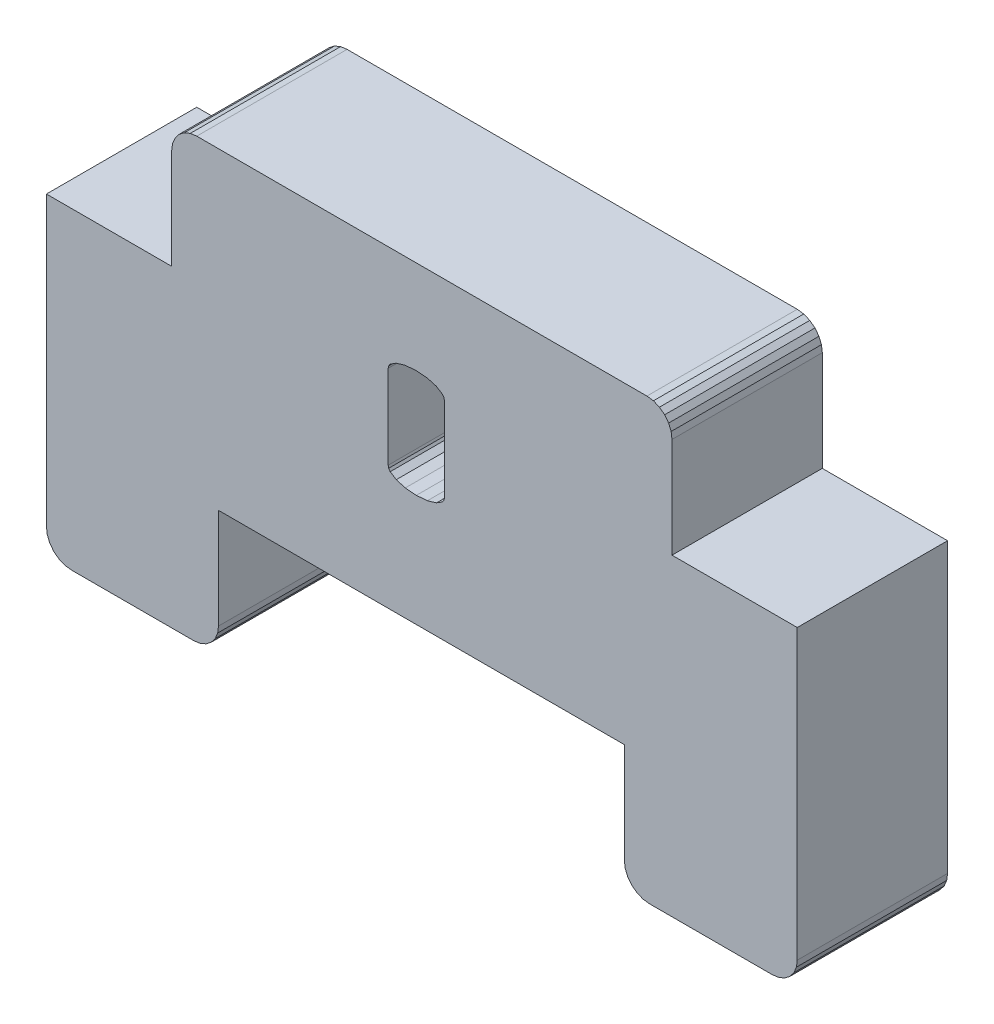
SolidWorks part; units mm, degrees
material "Maple"
ref_plane "Front Plane" through (0, 0, 0) normal (0, 0, 1) x (1, 0, 0)
ref_plane "Top Plane" through (0, 0, 0) normal (0, 1, 0) x (1, 0, 0)
ref_plane "Right Plane" through (0, 0, 0) normal (1, 0, 0) x (0, 0, -1)
sketch "Sketch1" plane through (0, 0, 0) normal (0, 0, 1) x (1, 0, 0)
  line L271 (-389.2048, -169.8544) -> (-389.1707, -169.5955)
  line L272 (-388.7048, -168.9883) -> (-388.4636, -168.8884)
  line L273 (-389.0708, -169.3544) -> (-388.9119, -169.1473)
  line L274 (-389.1707, -169.5955) -> (-389.0708, -169.3544)
  line L275 (-393.4636, -186.3203) -> (-393.7048, -186.2204)
  line L276 (-394.0708, -185.8544) -> (-394.1707, -185.6132)
  line L277 (-370.1363, -186.3544) -> (-370.3952, -186.3203)
  line L278 (-369.9775, -168.8884) -> (-370.2363, -168.8544)
  line L279 (-364.2363, -185.3544) -> (-364.2363, -173.8544)
  line L280 (-393.9119, -186.0615) -> (-394.0708, -185.8544)
  line L281 (-393.7048, -186.2204) -> (-393.9119, -186.0615)
  line L282 (-369.2363, -173.8544) -> (-364.2363, -173.8544)
  line L283 (-369.2363, -169.8544) -> (-369.2363, -173.8544)
  line L284 (-369.2363, -169.8544) -> (-369.2704, -169.5955)
  line L285 (-369.2704, -169.5955) -> (-369.3703, -169.3544)
  line L286 (-369.3703, -169.3544) -> (-369.5292, -169.1473)
  line L287 (-369.5292, -169.1473) -> (-369.7363, -168.9883)
  line L288 (-369.7363, -168.9883) -> (-369.9775, -168.8884)
  line L289 (-388.2048, -168.8544) -> (-370.2363, -168.8544)
  line L290 (-388.4636, -168.8884) -> (-388.2048, -168.8544)
  line L291 (-388.9119, -169.1473) -> (-388.7048, -168.9883)
  line L292 (-389.2048, -173.8544) -> (-389.2048, -169.8544)
  line L293 (-394.2048, -173.8544) -> (-389.2048, -173.8544)
  line L294 (-394.2048, -173.8544) -> (-394.2048, -185.3544)
  line L295 (-394.1707, -185.6132) -> (-394.2048, -185.3544)
  line L296 (-393.2048, -186.3544) -> (-393.4636, -186.3203)
  line L297 (-393.2048, -186.3544) -> (-388.3363, -186.3544)
  line L298 (-388.0775, -186.3203) -> (-388.3363, -186.3544)
  line L299 (-387.8363, -186.2204) -> (-388.0775, -186.3203)
  line L300 (-387.6292, -186.0615) -> (-387.8363, -186.2204)
  line L301 (-387.4703, -185.8544) -> (-387.6292, -186.0615)
  line L302 (-387.3704, -185.6132) -> (-387.4703, -185.8544)
  line L303 (-387.3363, -185.3544) -> (-387.3704, -185.6132)
  line L304 (-387.3363, -185.3544) -> (-387.3363, -181.3544)
  line L305 (-387.3363, -181.3544) -> (-371.1363, -181.3544)
  line L306 (-371.1363, -181.3544) -> (-371.1363, -185.3544)
  line L307 (-371.1023, -185.6132) -> (-371.1363, -185.3544)
  line L308 (-371.0024, -185.8544) -> (-371.1023, -185.6132)
  line L309 (-370.8434, -186.0615) -> (-371.0024, -185.8544)
  line L310 (-370.6363, -186.2204) -> (-370.8434, -186.0615)
  line L311 (-370.3952, -186.3203) -> (-370.6363, -186.2204)
  line L312 (-370.1363, -186.3544) -> (-365.2363, -186.3544)
  line L313 (-364.9775, -186.3203) -> (-365.2363, -186.3544)
  line L314 (-364.7363, -186.2204) -> (-364.9775, -186.3203)
  line L315 (-364.5292, -186.0615) -> (-364.7363, -186.2204)
  line L316 (-364.3703, -185.8544) -> (-364.5292, -186.0615)
  line L317 (-364.2704, -185.6132) -> (-364.3703, -185.8544)
  line L318 (-364.2363, -185.3544) -> (-364.2704, -185.6132)
  line L8527 (-380.5637, -176.4074) -> (-380.5436, -176.5036)
  line L8528 (-380.5436, -176.5036) -> (-380.4834, -176.5924)
  line L8529 (-380.4834, -176.5924) -> (-380.2422, -176.7477)
  line L8530 (-380.2422, -176.7477) -> (-379.8808, -176.853)
  line L8531 (-379.8808, -176.853) -> (-379.4398, -176.8882)
  line L8532 (-379.4398, -176.8882) -> (-378.9989, -176.853)
  line L8533 (-378.9989, -176.853) -> (-378.6375, -176.7477)
  line L8534 (-378.6375, -176.7477) -> (-378.3963, -176.5924)
  line L8535 (-378.3963, -176.5924) -> (-378.336, -176.5036)
  line L8536 (-378.336, -176.5036) -> (-378.3159, -176.4074)
  line L8537 (-378.3159, -176.4074) -> (-378.3159, -173.0607)
  line L8538 (-378.3159, -173.0607) -> (-378.336, -172.9645)
  line L8539 (-378.336, -172.9645) -> (-378.3963, -172.8757)
  line L8540 (-378.3963, -172.8757) -> (-378.6375, -172.7204)
  line L8541 (-378.6375, -172.7204) -> (-378.9989, -172.615)
  line L8542 (-378.9989, -172.615) -> (-379.4398, -172.5799)
  line L8543 (-379.4398, -172.5799) -> (-379.8808, -172.615)
  line L8544 (-379.8808, -172.615) -> (-380.2422, -172.7204)
  line L8545 (-380.2422, -172.7204) -> (-380.4834, -172.8757)
  line L8546 (-380.4834, -172.8757) -> (-380.5436, -172.9645)
  line L8547 (-380.5436, -172.9645) -> (-380.5637, -173.0607)
  line L8548 (-380.5637, -173.0607) -> (-380.5637, -176.4074)
  line L8549 (-378.3159, -176.4074) -> (-378.336, -176.5036)
  line L8550 (-378.336, -176.5036) -> (-378.3963, -176.5924)
  line L8551 (-378.3963, -176.5924) -> (-378.6375, -176.7477)
  line L8552 (-378.6375, -176.7477) -> (-378.9989, -176.853)
  line L8553 (-378.9989, -176.853) -> (-379.4398, -176.8882)
  line L8554 (-379.4398, -176.8882) -> (-379.8808, -176.853)
  line L8555 (-379.8808, -176.853) -> (-380.2422, -176.7477)
  line L8556 (-380.2422, -176.7477) -> (-380.4834, -176.5924)
  line L8557 (-380.4834, -176.5924) -> (-380.5436, -176.5036)
  line L8558 (-380.5436, -176.5036) -> (-380.5637, -176.4074)
  line L8559 (-380.5637, -176.4074) -> (-380.5637, -173.0607)
  line L8560 (-380.5637, -173.0607) -> (-380.5436, -172.9645)
  line L8561 (-380.5436, -172.9645) -> (-380.4834, -172.8757)
  line L8562 (-380.4834, -172.8757) -> (-380.2422, -172.7204)
  line L8563 (-380.2422, -172.7204) -> (-379.8808, -172.615)
  line L8564 (-379.8808, -172.615) -> (-379.4398, -172.5799)
  line L8565 (-379.4398, -172.5799) -> (-378.9989, -172.615)
  line L8566 (-378.9989, -172.615) -> (-378.6375, -172.7204)
  line L8567 (-378.6375, -172.7204) -> (-378.3963, -172.8757)
  line L8568 (-378.3963, -172.8757) -> (-378.336, -172.9645)
  line L8569 (-378.336, -172.9645) -> (-378.3159, -173.0607)
  line L8570 (-378.3159, -173.0607) -> (-378.3159, -176.4074)
  line L8571 (-379.2837, -176.2829) -> (-378.3222, -177.5006)
extrude "Boss-Extrude1" add sketch "Sketch1" along normal blind 6 contours L318 L279 L282 L283 L284 L285 L286 L287 L288 L278 L289 L290 L272 L291 L273 L274 L271 L292 L293 L294 L295 L276 L280 L281 L275 L296 L297 L298 L299 L300 L301 L302 L303 L304 L305 L306 L307 L308 L309 L310 L311 L277 L312 L313 L314 L315 L316 L317 L8548 L8547
